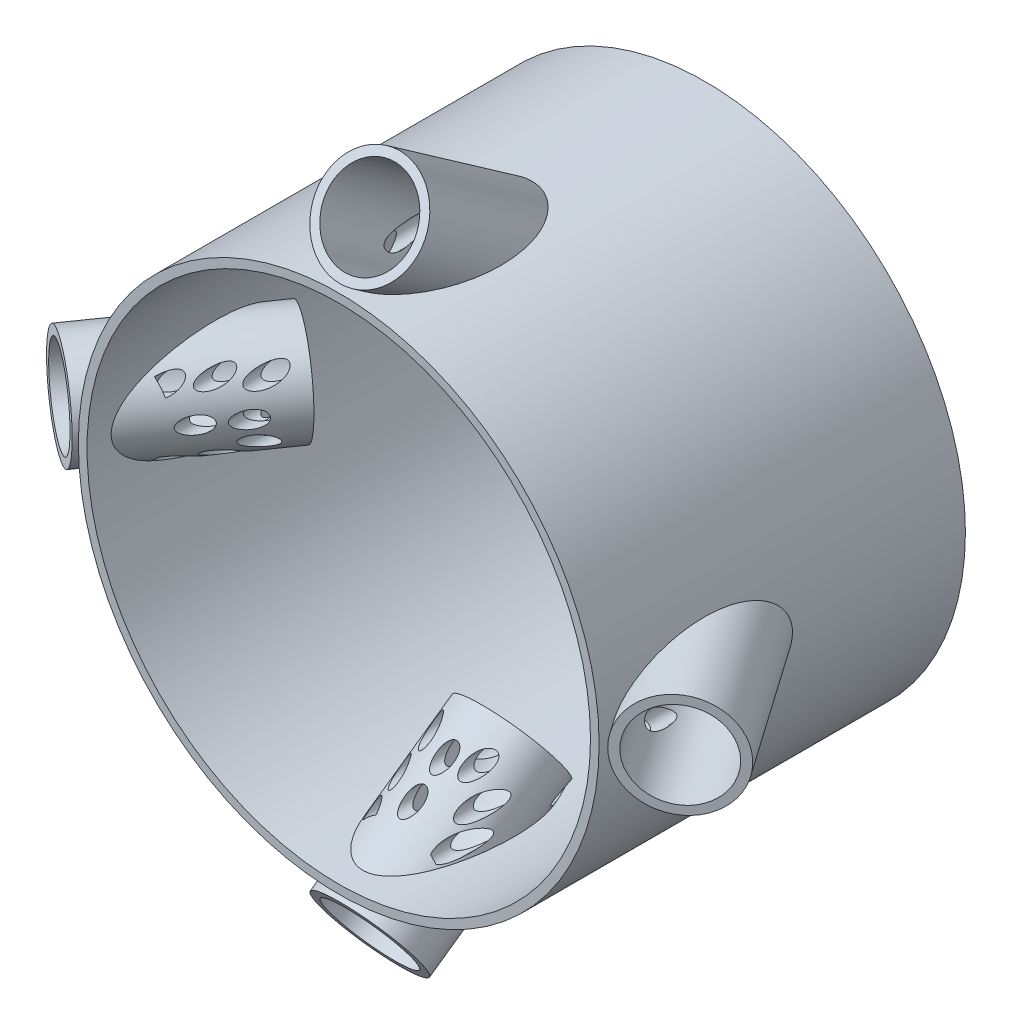
SolidWorks part; units mm, degrees
ref_plane "Front Plane" through (0, 0, 0) normal (0, 0, 1) x (1, 0, 0)
ref_plane "Top Plane" through (0, 0, 0) normal (0, 1, 0) x (1, 0, 0)
ref_plane "Right Plane" through (0, 0, 0) normal (1, 0, 0) x (0, 0, -1)
sketch "Sketch2" plane through (0, 0, 0) normal (0, 0, 1) x (1, 0, 0)
  circle A0 centre (0, 0) radius 300
  circle A1 centre (0, 0) radius 290
  dimension "D1" = 600
  dimension "D2" = 580
extrude "Boss-Extrude1" add sketch "Sketch2" along normal blind 405 and the other way blind 17
sketch "Sketch6" plane through (0, 0, 0) normal (0, 1, 0) x (1, 0, 0)
  line L0 (-300, -18.9501) -> (300, -18.9501) construction
  line L3 (-300, 17) -> (-300, -405) construction
  line L4 (300, -405) -> (300, 17) construction
  line L5 (-300, -18.9501) -> (116.8756, -310.8495) construction
  line L6 (300, -18.9501) -> (2.1564, -227.5024) construction
  line L7 (300, 17) -> (-300, 17) construction
  point P6 (-174.1248, -107.0889)
  point P9 (174.1248, -107.0889)
  dimension "D1" = 35
  dimension "D2" = 35
  dimension "D3" = 153.6653
  dimension "D4" = 153.6653
  dimension "D5" = 35.9501
ref_plane "Plane2" through (-107.6006, 0, 153.6696) normal (-0.5736, 0, 0.8192) x (0.8192, 0, 0.5736)
sketch "Sketch7" plane through (-107.6006, 0, 153.6696) normal (-0.5736, 0, 0.8192) x (0.8192, 0, 0.5736)
  circle A0 centre (-81.211, 0) radius 60
  circle A1 centre (-81.211, 0) radius 50
extrude "Boss-Extrude2" add sketch "Sketch7" along normal blind 320
sketch "Sketch8" plane through (-107.6006, 0, 153.6696) normal (-0.5736, 0, 0.8192) x (0.8192, 0, 0.5736)
  circle A0 centre (-81.211, 0) radius 60
  circle A1 centre (-81.211, 0) radius 50
extrude "Cut-Extrude1" cut sketch "Sketch8" along normal blind 120
sketch "Sketch9" plane through (-107.6006, 0, 153.6696) normal (-0.5736, 0, 0.8192) x (0.8192, 0, 0.5736)
  circle A0 centre (-81.211, 0) radius 50
extrude "Cut-Extrude2" cut sketch "Sketch9" along normal blind 1650
ref_plane "Plane3" through (107.6006, 0, 153.6696) normal (-0.5736, 0, -0.8192) x (-0.8192, 0, 0.5736)
sketch "Sketch10" plane through (107.6006, 0, 153.6696) normal (-0.5736, 0, -0.8192) x (-0.8192, 0, 0.5736)
  circle A1 centre (-81.211, 0) radius 60
  circle A2 centre (-81.211, 0) radius 50
extrude "Boss-Extrude3" add sketch "Sketch10" against normal blind 320
sketch "Sketch14" plane through (0, 0, 0) normal (1, 0, 0) x (0, 0, -1)
  line L0 (-18.9501, -300) -> (-18.9501, 300) construction
  line L1 (-405, -300) -> (17, -300) construction
  line L2 (17, 300) -> (-405, 300) construction
  line L3 (17, -300) -> (17, 300) construction
  line L4 (-18.9501, -300) -> (-266.6287, 53.7218) construction
  line L5 (-18.9501, 300) -> (-356.5675, -182.1676) construction
  point P8 (-107.0889, -174.1248)
  point P10 (-107.0889, 174.1248)
  dimension "D1" = 35.9501
  dimension "D2" = 35
  dimension "D3" = 35
  dimension "D4" = 153.6653
  dimension "D5" = 153.6653
ref_plane "Plane4" through (0, -107.6006, 153.6696) normal (0, 0.5736, -0.8192) x (0, 0.8192, 0.5736)
sketch "Sketch16" plane through (0, -107.6006, 153.6696) normal (0, 0.5736, -0.8192) x (0, 0.8192, 0.5736)
  circle A0 centre (-81.211, 0) radius 60
  circle A1 centre (-81.211, 0) radius 50
extrude "Boss-Extrude4" add sketch "Sketch16" against normal blind 320
sketch "Sketch17" plane through (0, -107.6006, 153.6696) normal (0, 0.5736, -0.8192) x (0, 0.8192, 0.5736)
  circle A0 centre (-81.211, 0) radius 50
  circle A1 centre (-81.211, 0) radius 60
extrude "Cut-Extrude3" cut sketch "Sketch17" against normal blind 120
sketch "Sketch18" plane through (0, -107.6006, 153.6696) normal (0, 0.5736, -0.8192) x (0, 0.8192, 0.5736)
  circle A0 centre (-81.211, 0) radius 50
extrude "Cut-Extrude4" cut sketch "Sketch18" against normal blind 600
sketch "Sketch19" plane through (107.6006, 0, 153.6696) normal (-0.5736, 0, -0.8192) x (-0.8192, 0, 0.5736)
  circle A0 centre (-81.211, 0) radius 50
extrude "Cut-Extrude5" cut sketch "Sketch19" against normal blind 600
ref_plane "Plane5" through (0, 107.6006, 153.6696) normal (0, 0.5736, 0.8192) x (0, -0.8192, 0.5736)
sketch "Sketch20" plane through (0, 107.6006, 153.6696) normal (0, 0.5736, 0.8192) x (0, -0.8192, 0.5736)
  circle A0 centre (-81.211, 0) radius 60
  circle A1 centre (-81.211, 0) radius 50
extrude "Boss-Extrude5" add sketch "Sketch20" along normal blind 320
sketch "Sketch21" plane through (0, 107.6006, 153.6696) normal (0, 0.5736, 0.8192) x (0, -0.8192, 0.5736)
  circle A0 centre (-81.211, 0) radius 60
  circle A1 centre (-81.211, 0) radius 50
extrude "Boss-Extrude6" add sketch "Sketch21" along normal blind 120
sketch "Sketch22" plane through (0, 107.6006, 153.6696) normal (0, 0.5736, 0.8192) x (0, -0.8192, 0.5736)
  circle A0 centre (-81.211, 0) radius 50
extrude "Cut-Extrude6" cut sketch "Sketch22" along normal blind 733
sketch "Sketch23" plane through (0, 107.6006, 153.6696) normal (0, 0.5736, 0.8192) x (0, -0.8192, 0.5736)
  circle A0 centre (-81.211, 0) radius 50
  circle A1 centre (-81.211, 0) radius 60
extrude "Cut-Extrude7" cut sketch "Sketch23" along normal blind 120
sketch "Sketch24" plane through (107.6006, 0, 153.6696) normal (-0.5736, 0, -0.8192) x (-0.8192, 0, 0.5736)
  circle A0 centre (-81.211, 0) radius 50
  circle A1 centre (-81.211, 0) radius 60
extrude "Cut-Extrude8" cut sketch "Sketch24" against normal blind 120
sketch "Sketch25" plane through (0, 0, 0) normal (0, 0, 1) x (1, 0, 0)
  circle A0 centre (0, 250.0972) radius 10
  circle A1 centre (36.9271, 250.0972) radius 8.952
  circle A2 centre (-43.6411, 250.0972) radius 10
  circle A3 centre (-26.8561, 224.3601) radius 10
  circle A4 centre (-46.5197, 273.9945) radius 10
  circle A5 centre (1, 276.6832) radius 8.952
  circle A6 centre (34.4349, 273.9945) radius 10
  circle A7 centre (34.4349, 224.3601) radius 10
  circle A8 centre (0, 224.3601) radius 10
  circle A9 centre (250.0972, 0) radius 10
  circle A10 centre (250.0972, -36.9271) radius 8.952
  circle A11 centre (250.0972, 43.6411) radius 10
  circle A12 centre (224.3601, 26.8561) radius 10
  circle A13 centre (273.9945, 46.5197) radius 10
  circle A14 centre (276.6832, -1) radius 8.952
  circle A15 centre (273.9945, -34.4349) radius 10
  circle A16 centre (224.3601, -34.4349) radius 10
  circle A17 centre (224.3601, 0) radius 10
  circle A18 centre (0, -250.0972) radius 10
  circle A19 centre (-36.9271, -250.0972) radius 8.952
  circle A20 centre (43.6411, -250.0972) radius 10
  circle A21 centre (26.8561, -224.3601) radius 10
  circle A22 centre (46.5197, -273.9945) radius 10
  circle A23 centre (-1, -276.6832) radius 8.952
  circle A24 centre (-34.4349, -273.9945) radius 10
  circle A25 centre (-34.4349, -224.3601) radius 10
  circle A26 centre (0, -224.3601) radius 10
  circle A27 centre (-250.0972, 0) radius 10
  circle A28 centre (-250.0972, 36.9271) radius 8.952
  circle A29 centre (-250.0972, -43.6411) radius 10
  circle A30 centre (-224.3601, -26.8561) radius 10
  circle A31 centre (-273.9945, -46.5197) radius 10
  circle A32 centre (-276.6832, 1) radius 8.952
  circle A33 centre (-273.9945, 34.4349) radius 10
  circle A34 centre (-224.3601, 34.4349) radius 10
  circle A35 centre (-224.3601, 0) radius 10
  ellipse E0 centre (0, 242.9539) end of major axis (60, 242.9539) minor radius 49.1491 (-19.9212, 289.315) -> (19.9212, 289.315) ccw construction
  dimension "D1" = 4
extrude "Cut-Extrude9" cut sketch "Sketch25" along normal blind 336
